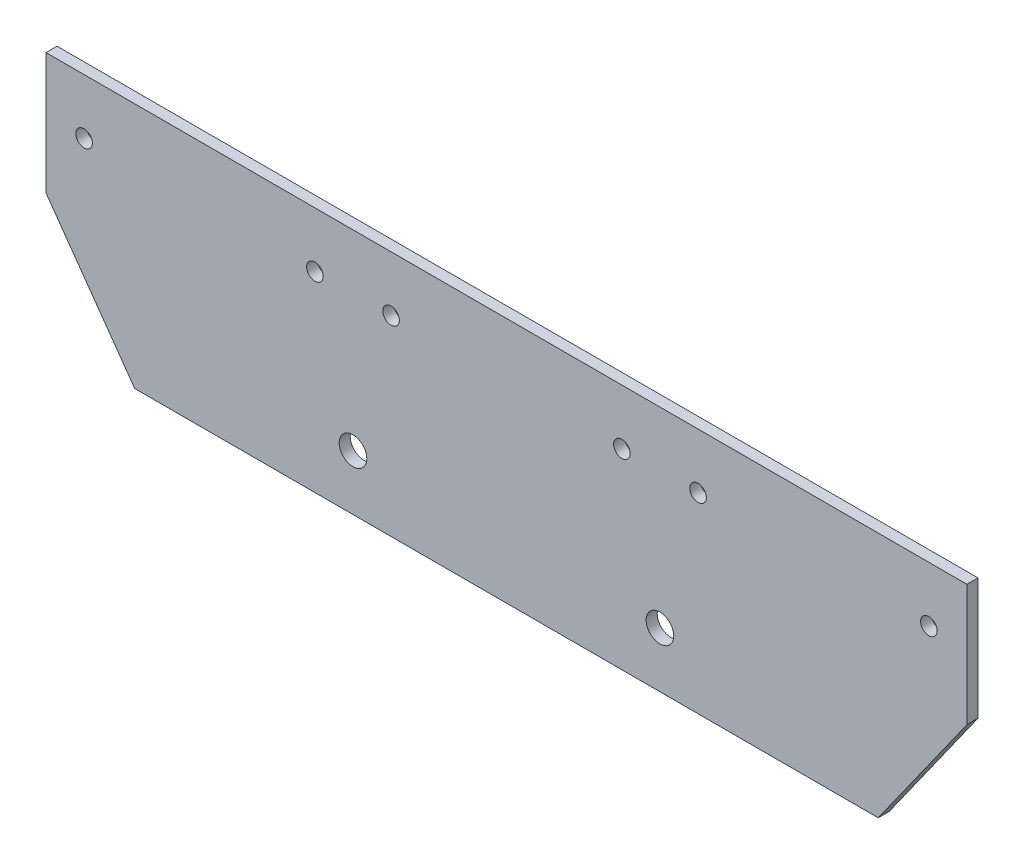
SolidWorks part; units mm, degrees
ref_plane "Front Plane" through (0, 0, 0) normal (0, 0, 1) x (1, 0, 0)
ref_plane "Top Plane" through (0, 0, 0) normal (0, 1, 0) x (1, 0, 0)
ref_plane "Right Plane" through (0, 0, 0) normal (1, 0, 0) x (0, 0, -1)
sketch "Sketch1" plane through (0, 0, 0) normal (0, 0, 1) x (1, 0, 0)
  line L0 (-46.3475, 32.6429) -> (-22.8975, 32.6429) construction
  line L1 (-46.3475, 32.6429) -> (-22.8975, 32.6429)
  line L3 (-62.4029, 55.2729) -> (-46.3475, 32.6429)
  line L4 (-22.8975, 32.6429) -> (88.2241, 32.6429)
  line L5 (-62.4029, 55.2729) -> (-6.8421, 55.2729)
  line L7 (-6.8421, 55.2729) -> (-6.8421, 77.2729)
  line L8 (-6.8421, 77.2729) -> (-62.4029, 77.2729)
  line L11 (-62.4029, 77.2729) -> (-62.4029, 55.2729)
  line L28 (-6.8421, 77.2729) -> (-62.4029, 77.2729)
  line L36 (-62.4029, 77.2729) -> (-62.4029, 55.2729)
  line L39 (-6.8421, 55.2729) -> (48.7187, 55.2729)
  line L44 (48.7187, 55.2729) -> (48.7187, 77.2729)
  line L45 (48.7187, 77.2729) -> (-6.8421, 77.2729)
  line L53 (-6.8421, 77.2729) -> (-6.8421, 55.2729)
  line L56 (48.7187, 77.2729) -> (-6.8421, 77.2729)
  line L58 (48.7187, 55.2729) -> (104.2795, 55.2729)
  line L59 (104.2795, 55.2729) -> (104.2795, 77.2729)
  line L60 (104.2795, 77.2729) -> (48.7187, 77.2729)
  line L61 (48.7187, 77.2729) -> (48.7187, 55.2729)
  line L62 (48.7187, 55.2729) -> (104.2795, 55.2729)
  line L63 (104.2795, 55.2729) -> (104.2795, 77.2729)
  line L64 (104.2795, 77.2729) -> (48.7187, 77.2729)
  line L66 (104.2795, 55.2729) -> (88.2241, 32.6429)
  circle A12 centre (97.3893, 67.2729) radius 1.5 construction
  circle A13 centre (55.6089, 67.2729) radius 1.5 construction
  circle A14 centre (41.8285, 67.2729) radius 1.5 construction
  circle A15 centre (0.0481, 67.2729) radius 1.5 construction
  circle A16 centre (-13.7323, 67.2729) radius 1.5 construction
  circle A17 centre (-55.5127, 67.2729) radius 1.5 construction
  circle A18 centre (97.3893, 67.2729) radius 1.5
  circle A19 centre (55.6089, 67.2729) radius 1.5
  circle A20 centre (41.8285, 67.2729) radius 1.5
  circle A21 centre (0.0481, 67.2729) radius 1.5
  circle A22 centre (-13.7323, 67.2729) radius 1.5
  circle A23 centre (-55.5127, 67.2729) radius 1.5
  dimension "D3" = 0
  dimension "D1" = 0
  dimension "D2" = 0
extrude "Boss-Extrude1" add sketch "Sketch1" along normal blind 2
sketch "Sketch3" plane through (0, 0, 0) normal (0, 0, -1) x (-1, 0, 0)
  line L0 (-55.6089, 67.2729) -> (-41.8285, 67.2729) construction
  line L1 (-48.7187, 67.2729) -> (-48.7187, 32.6429) construction
  line L2 (-20.9383, 77.2729) -> (-20.9383, 32.6429) construction
  line L6 (-104.2795, 55.2729) -> (-88.2241, 32.6429)
  line L7 (-88.2241, 32.6429) -> (46.3475, 32.6429)
  line L8 (46.3475, 32.6429) -> (62.4029, 55.2729)
  line L9 (62.4029, 55.2729) -> (62.4029, 77.2729)
  line L10 (62.4029, 77.2729) -> (-104.2795, 77.2729)
  line L11 (-104.2795, 77.2729) -> (-104.2795, 55.2729)
  line L12 (-104.2795, 55.2729) -> (-88.2241, 32.6429) construction
  line L13 (-88.2241, 32.6429) -> (46.3475, 32.6429) construction
  line L14 (46.3475, 32.6429) -> (62.4029, 55.2729) construction
  line L15 (62.4029, 55.2729) -> (62.4029, 77.2729) construction
  line L16 (62.4029, 77.2729) -> (-104.2795, 77.2729) construction
  line L17 (-104.2795, 77.2729) -> (-104.2795, 55.2729) construction
  circle A0 centre (-97.3893, 67.2729) radius 1.5 construction
  circle A1 centre (-55.6089, 67.2729) radius 1.5 construction
  circle A2 centre (-41.8285, 67.2729) radius 1.5 construction
  circle A3 centre (-0.0481, 67.2729) radius 1.5 construction
  circle A4 centre (55.5127, 67.2729) radius 1.5 construction
  circle A5 centre (13.7323, 67.2729) radius 1.5 construction
  circle A6 centre (55.5127, 67.2729) radius 1.5 construction
  circle A7 centre (13.7323, 67.2729) radius 1.5 construction
  circle A8 centre (-0.0481, 67.2729) radius 1.5 construction
  circle A9 centre (-41.8285, 67.2729) radius 1.5 construction
  circle A10 centre (-55.6089, 67.2729) radius 1.5 construction
  circle A11 centre (-97.3893, 67.2729) radius 1.5 construction
  circle A12 centre (-48.7187, 42.6429) radius 2.5
  circle A13 centre (6.8421, 42.6429) radius 2.5
  dimension "D2" = 5
  dimension "D3" = 10
  dimension "D1" = 0
extrude "Cut-Extrude1" cut sketch "Sketch3" against normal up to surface (2 mm away) up to face at (20.9383, 55.0629, 2)
ref_plane "Plane1" through (20.9383, 0, 0) normal (1, 0, 0) x (0, 0, -1)
equation "\"T\"=2"
equation "\"D2@Sketch2\"=\"T\""
equation "\"C\"=0.15"
equation "\"D1@Sketch2\"=\"C\""
equation "\"D4@Sketch2\"=\"C\""
equation "\"D3@Sketch2\"=\"T\""
